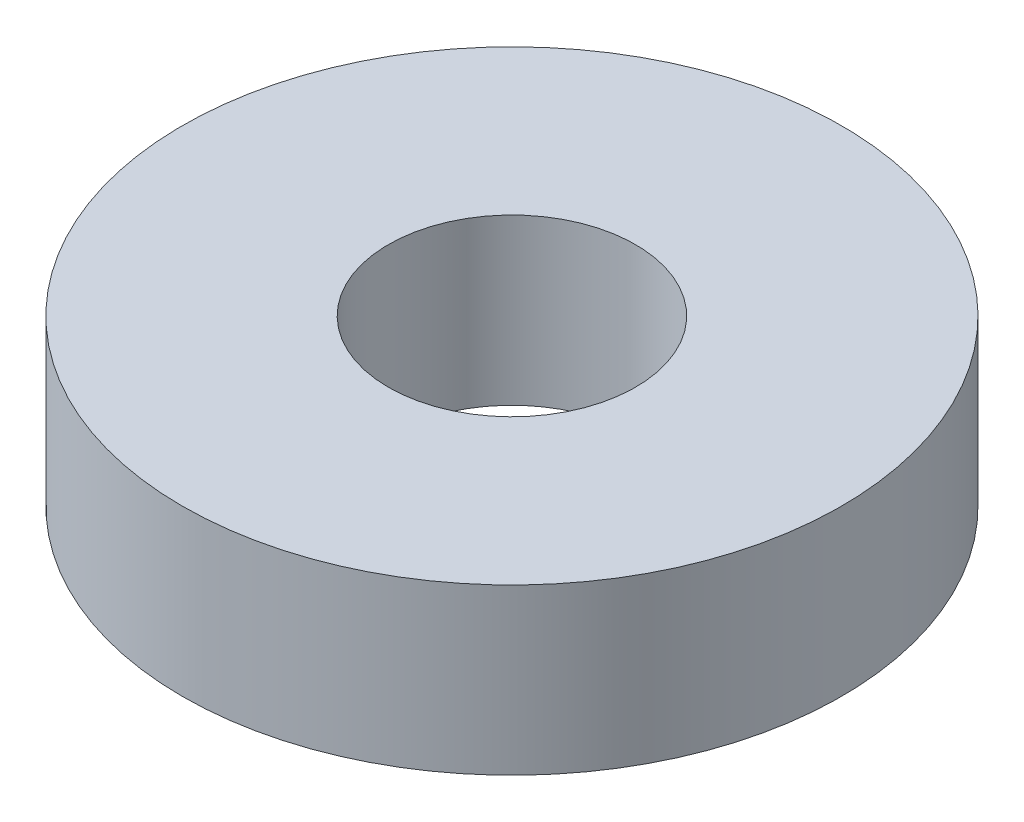
SolidWorks part; units mm, degrees
ref_plane "前视基准面" through (0, 0, 0) normal (0, 0, 1) x (1, 0, 0)
ref_plane "上视基准面" through (0, 0, 0) normal (0, 1, 0) x (1, 0, 0)
ref_plane "右视基准面" through (0, 0, 0) normal (1, 0, 0) x (0, 0, -1)
sketch "草图1" plane through (0, 0, 0) normal (0, 1, 0) x (1, 0, 0)
  circle A0 centre (0, 0) radius 20
  circle A1 centre (0, 0) radius 7.5
  dimension "D1" = 40
  dimension "D2" = 15
extrude "凸台-拉伸1" add sketch "草图1" along normal blind 10
